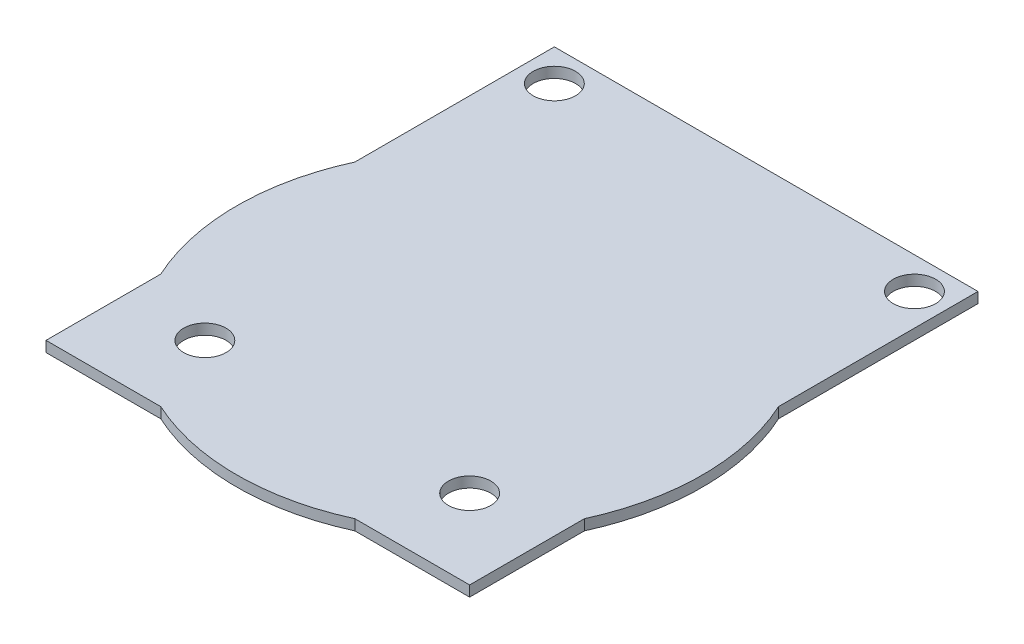
SolidWorks part; units mm, degrees
ref_plane "Front Plane" through (0, 0, 0) normal (0, 0, 1) x (1, 0, 0)
ref_plane "Top Plane" through (0, 0, 0) normal (0, 1, 0) x (1, 0, 0)
ref_plane "Right Plane" through (0, 0, 0) normal (1, 0, 0) x (0, 0, -1)
sketch "Sketch1" plane through (0, 0, 0) normal (0, 1, 0) x (1, 0, 0)
  line L0 (-28.7979, 18.1724) -> (13.2021, 18.1724)
  line L1 (-28.7979, 18.1724) -> (-28.7979, -31.8276)
  line L2 (-28.7979, -31.8276) -> (13.2021, -31.8276)
  line L3 (13.2021, 18.1724) -> (13.2021, -31.8276)
  line L4 (-16.7979, 18.1724) -> (-16.7979, 17.1724)
  line L5 (-16.7979, -19.8276) -> (1.2021, -19.8276)
  line L6 (1.2021, 18.1724) -> (1.2021, 17.1724)
  line L7 (-16.7979, 18.1724) -> (1.2021, 18.1724)
  line L8 (1.2021, 17.1724) -> (1.2021, -19.8276)
  line L9 (-16.7979, 17.1724) -> (-16.7979, -19.8276)
  line L10 (-27.7979, 17.1724) -> (12.2021, 17.1724)
  line L11 (12.2021, 17.1724) -> (12.2021, -30.8276)
  line L12 (-27.7979, -30.8276) -> (12.2021, -30.8276)
  line L13 (-27.7979, 17.1724) -> (-27.7979, -30.8276)
  circle A0 centre (-7.7979, -10.8276) radius 23
  circle A1 centre (-24.7979, 14.1724) radius 2
  circle A2 centre (-20.2979, -23.3276) radius 2
  circle A3 centre (9.2021, 14.1724) radius 2
  circle A4 centre (4.7021, -23.3276) radius 2
  circle A5 centre (-7.7979, -10.8276) radius 22
  dimension "D3" = 40
  dimension "D4" = 50
  dimension "D1" = 1
  dimension "D2" = 1
extrude "Boss-Extrude1" add sketch "Sketch1" along normal blind 1 contours A0 L11 L10 L13 L9 L4 L7 L6 L8 A1 A3 | L12 A5 L11 L8 L5 L9 L13 A2 A4 | L8 A5 L9 L5 | L11 A5 L3 | L3 A5 | A5 L11 A0 L8 | A5 L8 A0 L9 | A5 L9 A0 L13 | L13 A5 L1 | L1 A5 | L2 A5 | L2 A5 L12 | A0 L12 L11 | A5 L12 A0 L11 | A0 L13 L12 | A5 L13 A0 L12 | A0 L9 L10 L13 A1 | A0 L11 L10 L8 A3
